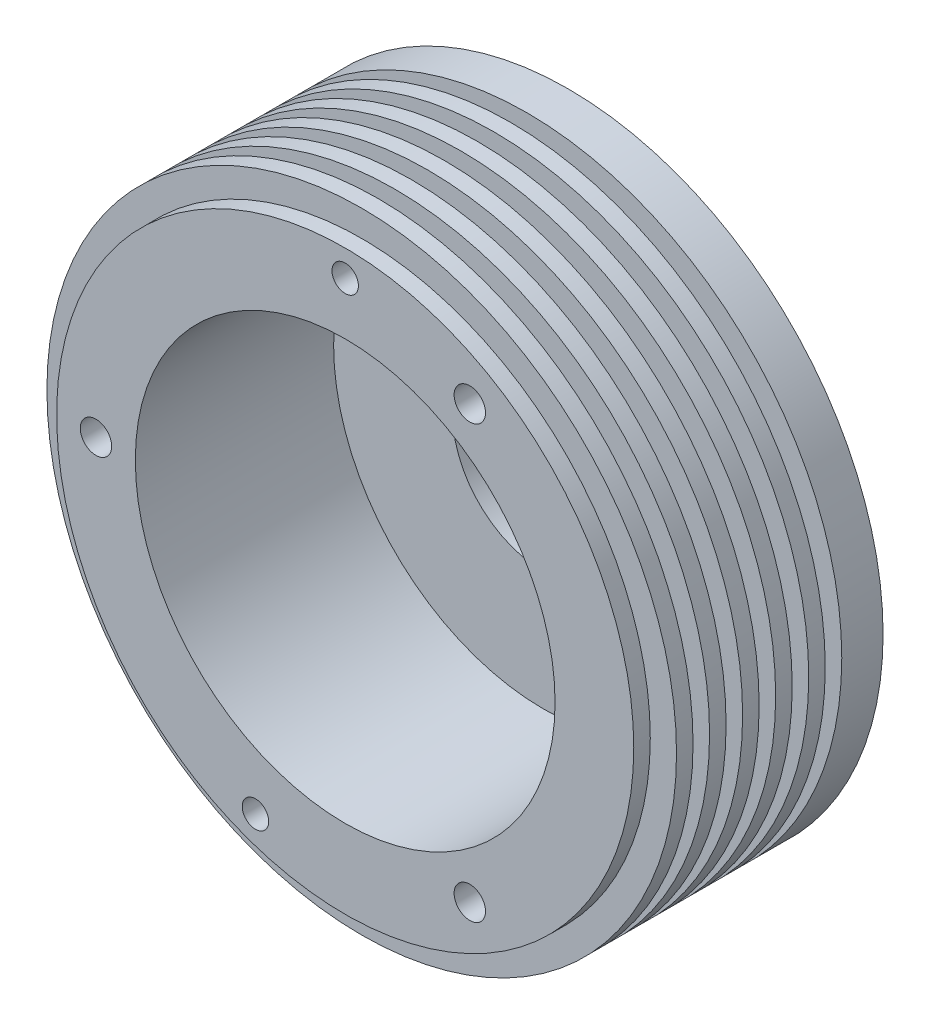
SolidWorks part; units mm, degrees
material "Alliage 1060"
ref_plane "Plan de face" through (0, 0, 0) normal (0, 0, 1) x (1, 0, 0)
ref_plane "Plan de dessus" through (0, 0, 0) normal (0, 1, 0) x (1, 0, 0)
ref_plane "Plan de droite" through (0, 0, 0) normal (1, 0, 0) x (0, 0, -1)
sketch "Esquisse1" plane through (0, 0, 0) normal (0, 0, 1) x (1, 0, 0)
  circle A0 centre (23.6795, 29.6707) radius 38.1
  dimension "D1" = 76.2
extrude "Boss.-Extru.1" add sketch "Esquisse1" along normal blind 27 contours A0
sketch "Esquisse3" plane through (0, 0, 27) normal (0, 0, 1) x (1, 0, 0)
  circle A0 centre (23.6795, 29.6707) radius 25.4
  dimension "D1" = 50.8
extrude "Enlèv. mat.-Extru.2" cut sketch "Esquisse3" against normal offset from surface (24 mm away) 3 up to face at (61.7795, 29.6707, 0)
sketch "Esquisse5" plane through (0, 0, 0) normal (0, 0, -1) x (-1, 0, 0)
  line L0 (-23.6795, 67.7707) -> (-23.6795, -8.4293) construction
  circle A0 centre (-23.6795, 29.6707) radius 11
  circle A1 centre (-23.6795, 29.6707) radius 38.1 construction
  point P7 (-23.6795, 29.6707)
  dimension "D1" = 22
extrude "Enlèv. mat.-Extru.3" cut sketch "Esquisse5" against normal up to surface (3 mm away) contours A0 up to face at (49.0795, 29.6707, 3)
sketch "Esquisse8" plane through (0, 0, 27) normal (0, 0, 1) x (1, 0, 0)
  circle A0 centre (23.6795, 29.6707) radius 34.925
  circle A1 centre (23.6795, 29.6707) radius 38.1
  dimension "D1" = 3.175
extrude "Enlèv. mat.-Extru.5" cut sketch "Esquisse8" against normal blind 2
pattern_linear "Répétition linéaire1" count 6 spacing 4 along (0, 0, -1) of "Enlèv. mat.-Extru.5"
sketch "Esquisse9" plane through (0, 0, 0) normal (0, 0, -1) x (-1, 0, 0)
  line L0 (-61.7795, 29.6707) -> (14.4205, 29.6707) construction
  circle A0 centre (6.483, 29.6707) radius 1.8
  circle A1 centre (-23.6795, 29.6707) radius 38.1 construction
  circle A2 centre (-38.7608, 3.5492) radius 1.8
  circle A3 centre (-38.7608, 55.7922) radius 1.8
  point P7 (-23.6795, 29.6707)
  point P12 (-23.6795, 29.6707)
  dimension "D1" = 3.6
  dimension "D2" = 30.1625
  dimension "D3" = 3
hole_wizard "Dégagement #61" positions "Esquisse10" profile "Esquisse11" hole size "#6" standard "Ansi Inch" end condition through all
sketch "Esquisse10" plane through (0, 0, 0) normal (0, 0, -1) x (-1, 0, 0)
  point P0 (-38.7608, 55.7922)
  point P3 (6.483, 29.6707)
  point P6 (-38.7608, 3.5492)
sketch "Esquisse11" plane through (38.7608, 55.7922, 0) normal (1, 0, 0) x (0, 1, 0)
  line L0 (0, 0) -> (0, 27)
  line L1 (0, 27) -> (1.8986, 27)
  line L2 (1.8986, 27) -> (1.8986, 0)
  line L5 (1.8986, 0) -> (0, 0)
  line L11 (0, -6.35) -> (0, 107.95) construction
  dimension "Diamètre du perçage jusqu'au prochain" = 3.7973
  dimension "Profondeur du perçage jusqu'au prochain" = 27
sketch "Esquisse15" plane through (0, 0, 0) normal (0, 0, -1) x (-1, 0, 0)
  line L0 (-23.6795, 29.6707) -> (-23.6795, 61.4207) construction
  line L1 (-23.6795, 29.6707) -> (-12.8204, -0.1645) construction
  dimension "D1" = 31.75
hole_wizard "1/8 (0.126) Trous de centrage1" positions "Esquisse17" profile "Esquisse18" hole size "1/8" standard "Ansi Inch"
sketch "Esquisse17" plane through (0, 0, 0) normal (0, 0, -1) x (-1, 0, 0)
  point P0 (-23.6795, 61.4207)
  point P3 (-12.8204, -0.1645)
sketch "Esquisse18" plane through (23.6795, 61.4207, 0) normal (1, 0, 0) x (0, 1, 0)
  line L0 (0, 0) -> (0, 27.9615)
  line L1 (0, 27.9615) -> (1.6002, 27)
  line L2 (1.6002, 27) -> (1.6002, 0)
  line L5 (1.6002, 0) -> (0, 0)
  line L10 (0, 27.9615) -> (-1.6002, 27) construction
  line L11 (0, -6.35) -> (0, 107.95) construction
  dimension "Diamètre du perçage" = 3.2004
  dimension "Profondeur du perçage" = 27
  dimension "Angle de pointe" = 118
